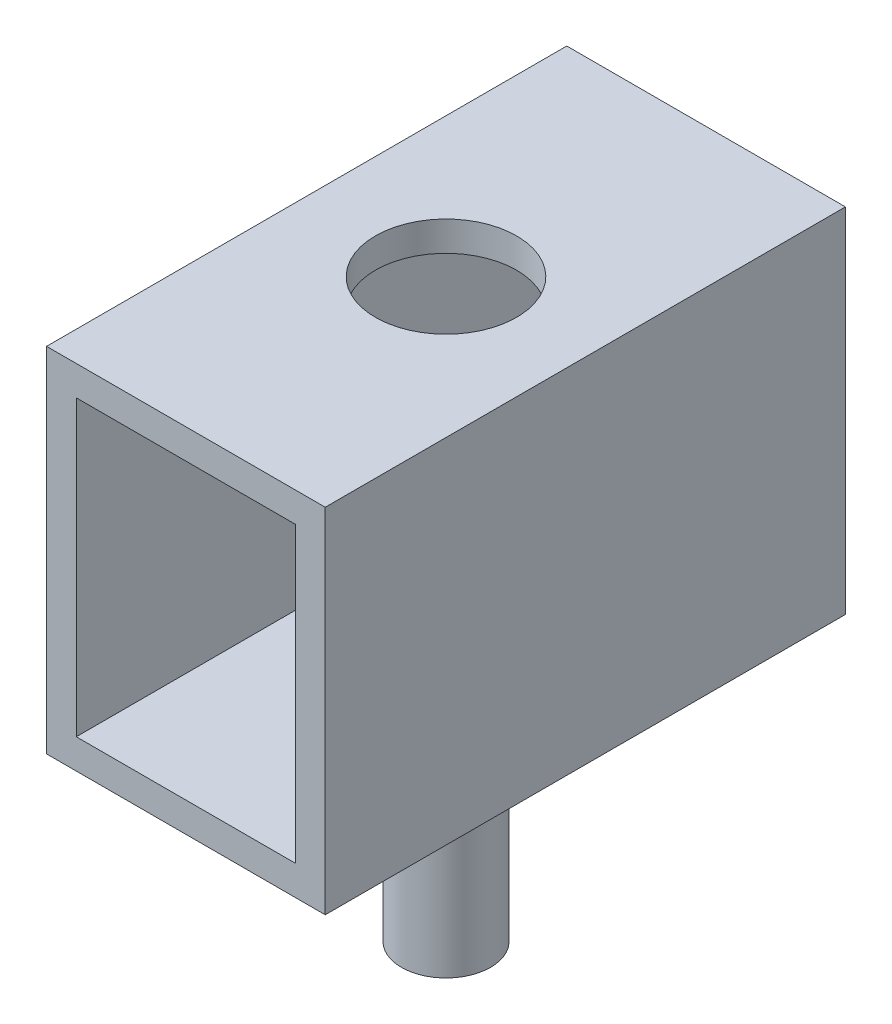
SolidWorks part; units mm, degrees
ref_plane "Front Plane" through (0, 0, 0) normal (0, 0, 1) x (1, 0, 0)
ref_plane "Top Plane" through (0, 0, 0) normal (0, 1, 0) x (1, 0, 0)
ref_plane "Right Plane" through (0, 0, 0) normal (1, 0, 0) x (0, 0, -1)
sketch "Sketch1" plane through (0, 0, 0) normal (0, 0, 1) x (1, 0, 0)
  line L0 (-1.475, -1.475) -> (-1.475, 2.475)
  line L1 (1.875, -1.875) -> (-1.875, -1.875)
  line L2 (1.875, -1.875) -> (1.875, 2.875)
  line L3 (1.875, 2.875) -> (-1.875, 2.875)
  line L4 (-1.875, -1.875) -> (-1.875, 2.875)
  line L5 (1.875, -1.875) -> (-1.875, 2.875) construction
  line L6 (1.875, 2.875) -> (-1.875, -1.875) construction
  line L7 (1.475, 2.475) -> (-1.475, 2.475)
  line L8 (1.475, -1.475) -> (1.475, 2.475)
  line L9 (1.475, -1.475) -> (-1.475, -1.475)
  dimension "D1" = 4.75
  dimension "D3" = 3.75
  dimension "D4" = 0.4
extrude "Boss-Extrude1" add sketch "Sketch1" along normal blind 7
ref_plane "Plane1" through (0, -1.875, 0) normal (0, -1, 0) x (-1, 0, 0)
sketch "Sketch2" plane through (0, -1.875, 0) normal (0, -1, 0) x (-1, 0, 0)
  line L1 (1.875, -7) -> (-1.875, -7) construction
  line L2 (1.875, 0) -> (-1.875, 0) construction
  circle A0 centre (0, -3.5) radius 0.6
extrude "Boss-Extrude2" add sketch "Sketch2" along normal blind 3 separate body
ref_plane "Plane2" through (0, 2.875, 0) normal (0, 1, 0) x (1, 0, 0)
sketch "Sketch3" plane through (0, 2.875, 0) normal (0, 1, 0) x (1, 0, 0)
  circle A0 centre (0, -3.5) radius 0.95
  circle A1 centre (0, -3.5) radius 0.6 construction
  dimension "D1" = 1.9
extrude "Cut-Extrude4" cut sketch "Sketch3" against normal up to surface (0.4 mm away) up to face at (0, 2.475, 3.5)
equation "\"D2@Sketch2\"=\"D1@Sketch2\"/2"
